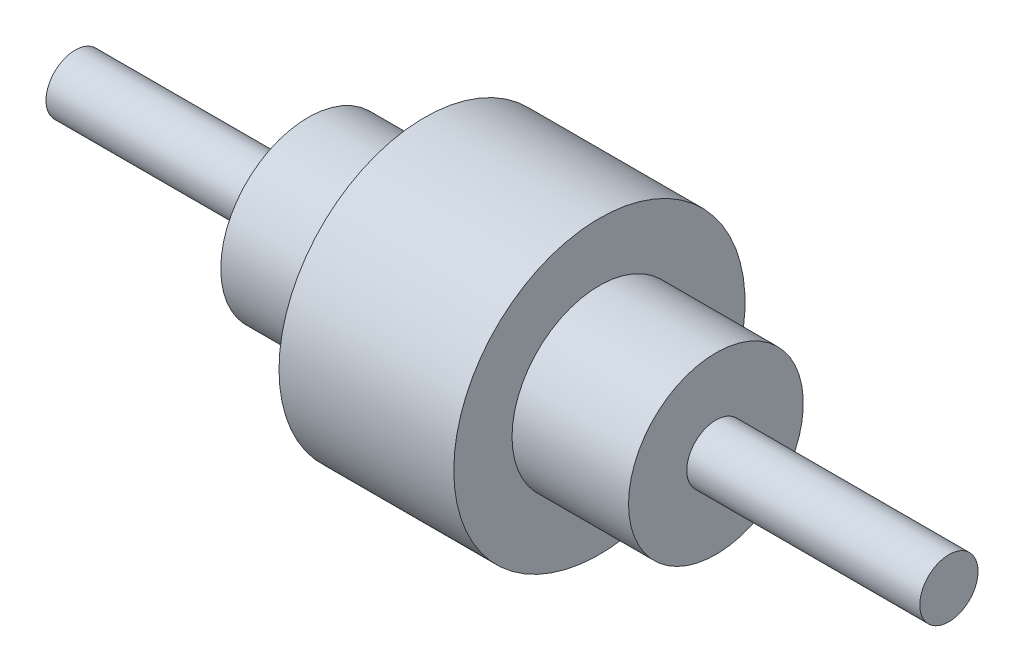
SolidWorks part; units mm, degrees
ref_plane "Front Plane" through (0, 0, 0) normal (0, 0, 1) x (1, 0, 0)
ref_plane "Top Plane" through (0, 0, 0) normal (0, 1, 0) x (1, 0, 0)
ref_plane "Right Plane" through (0, 0, 0) normal (1, 0, 0) x (0, 0, -1)
sketch "Sketch1" plane through (0, 0, 0) normal (0, 0, 1) x (1, 0, 0)
  line L0 (0, 0) -> (144.5984, 0) construction
  line L1 (0, 10) -> (0, 0)
  line L2 (0, 10) -> (80, 10)
  line L3 (80, 10) -> (80, 30)
  line L4 (80, 30) -> (120, 30)
  line L5 (120, 30) -> (120, 50)
  line L6 (120, 50) -> (180, 50)
  line L7 (150, 50) -> (150, 0) construction
  line L8 (300, 0) -> (155.4016, 0) construction
  line L9 (180, 30) -> (180, 50)
  line L10 (220, 10) -> (220, 30)
  line L11 (300, 10) -> (220, 10)
  line L12 (300, 10) -> (300, 0)
  line L13 (220, 30) -> (180, 30)
  line L14 (0, 0) -> (300, 0)
  dimension "D1" = 10
  dimension "D2" = 80
  dimension "D3" = 150
  dimension "D4" = 30
  dimension "D5" = 20
  dimension "D6" = 50
  dimension "D7" = 30
revolve "Revolve1" add sketch "Sketch1" angle 360 about L14
